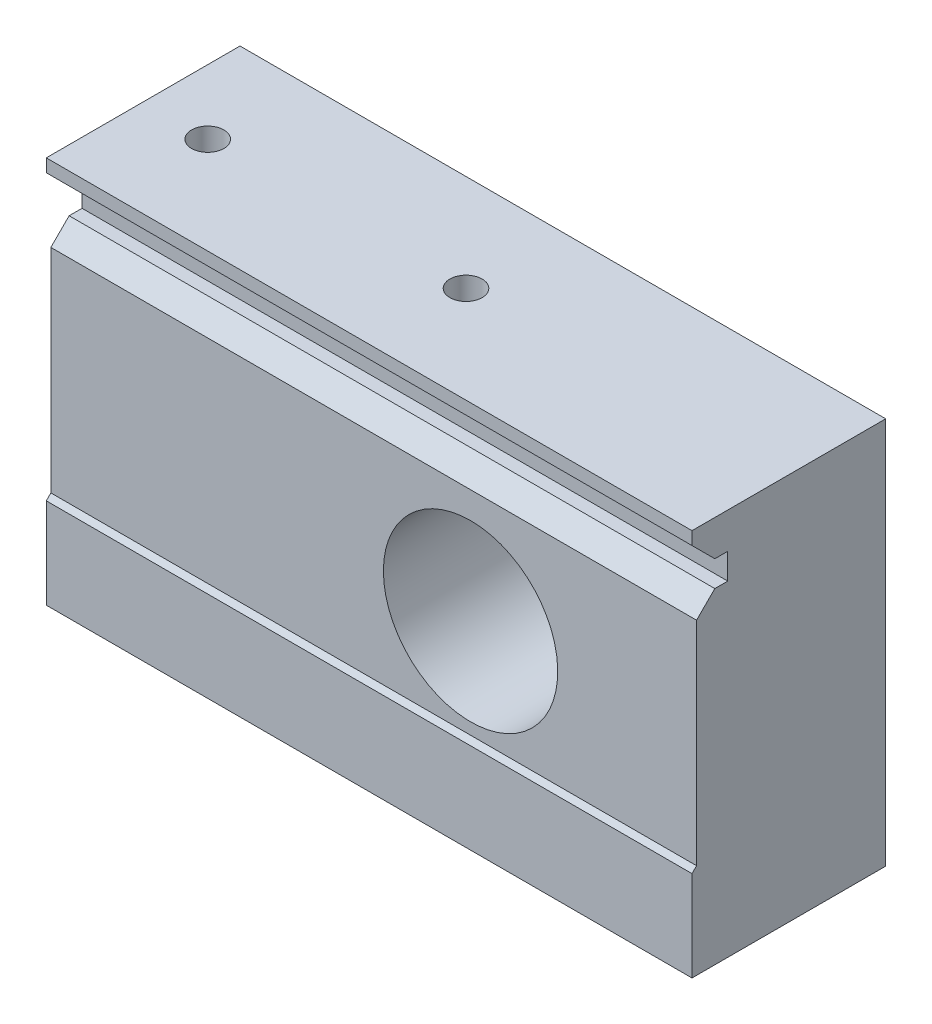
SolidWorks part; units mm, degrees
ref_plane "Front Plane" through (0, 0, 0) normal (0, 0, 1) x (1, 0, 0)
ref_plane "Top Plane" through (0, 0, 0) normal (0, 1, 0) x (1, 0, 0)
ref_plane "Right Plane" through (0, 0, 0) normal (1, 0, 0) x (0, 0, -1)
sketch "Sketch1" plane through (0, 0, 0) normal (0, 0, 1) x (1, 0, 0)
  line L1 (-47.9208, 29.5149) -> (52.0792, 29.5149)
  line L2 (-47.9208, 29.5149) -> (-47.9208, -30.4851)
  line L3 (-47.9208, -30.4851) -> (52.0792, -30.4851)
  line L4 (52.0792, 29.5149) -> (52.0792, -30.4851)
  dimension "D1" = 100
  dimension "D2" = 60
extrude "Boss-Extrude1" add sketch "Sketch1" along normal blind 30
sketch "Sketch3" plane through (-47.9208, 0, 0) normal (-1, 0, 0) x (0, 0, 1)
  line L10 (30, -30.4851) -> (30, -16.4851)
  line L11 (30, 29.5149) -> (30, -30.4851) construction
  line L12 (30, -16.4851) -> (29.2929, -15.778)
  line L13 (29.2929, -15.778) -> (29.2929, 17.1509)
  line L14 (29.2929, 17.1509) -> (26.4645, 19.9793)
  line L15 (26.4645, 19.9793) -> (24.4645, 19.9793)
  line L16 (24.4645, 19.9793) -> (24.4645, 23.9793)
  line L17 (24.4645, 23.9793) -> (26.4645, 23.9793)
  line L18 (26.4645, 23.9793) -> (30, 27.5149)
  line L19 (30, 27.5149) -> (30, 29.5149)
  line L20 (30, 29.5149) -> (35.631, 28.6016)
  line L21 (35.631, 28.6016) -> (37.1491, -26.2478)
  line L22 (37.1491, -26.2478) -> (30, -30.4851)
  dimension "D1" = 2
  dimension "D2" = 4
  dimension "D3" = 5
  dimension "D4" = 4
  dimension "D5" = 2
  dimension "D6" = 135
  dimension "D7" = 14
extrude "Cut-Extrude1" cut sketch "Sketch3" against normal blind 110
sketch "Эскиз1" plane through (0, 29.5149, 0) normal (0, 1, 0) x (1, 0, 0)
  line L0 (52.0792, 0) -> (-47.9208, 0) construction
  line L1 (52.0792, -30) -> (52.0792, 0) construction
  circle A0 centre (2.0792, -15) radius 2.5
  dimension "D2" = 50
  dimension "D1" = 15
extrude "Вырез-Вытянуть1" cut sketch "Эскиз1" against normal blind 10
pattern_linear "Линейный массив1" count 2 spacing 40 along (-1, 0, 0) count 2 spacing 50 along (0, -1, 0) of "Вырез-Вытянуть1"
sketch "Эскиз2" plane through (0, 0, 0) normal (0, 0, -1) x (-1, 0, 0)
  line L0 (-52.0792, 29.5149) -> (47.9208, 29.5149) construction
  line L1 (-52.0792, -30.4851) -> (-52.0792, 29.5149) construction
  circle A0 centre (-17.0792, -0.4851) radius 13.5
  dimension "D1" = 30
  dimension "D2" = 35
extrude "Вырез-Вытянуть2" cut sketch "Эскиз2" against normal blind 100
